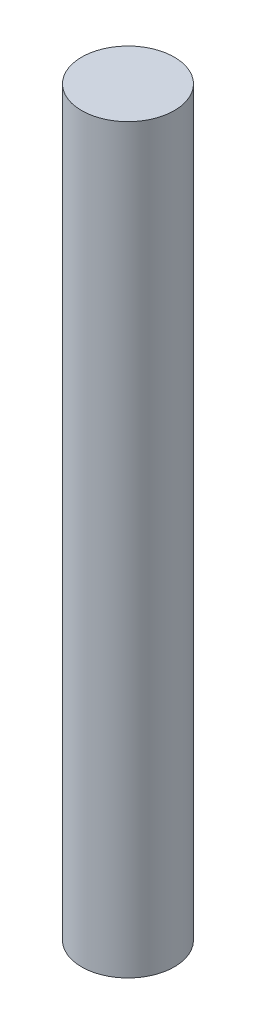
SolidWorks part; units mm, degrees
ref_plane "Front Plane" through (0, 0, 0) normal (0, 0, 1) x (1, 0, 0)
ref_plane "Top Plane" through (0, 0, 0) normal (0, 1, 0) x (1, 0, 0)
ref_plane "Right Plane" through (0, 0, 0) normal (1, 0, 0) x (0, 0, -1)
sketch "Sketch1" plane through (0, 0, 0) normal (0, 1, 0) x (1, 0, 0)
  circle A0 centre (0, 0) radius 1.5875
  dimension "D1" = 3.175
extrude "Boss-Extrude1" add sketch "Sketch1" against normal blind 25.4
